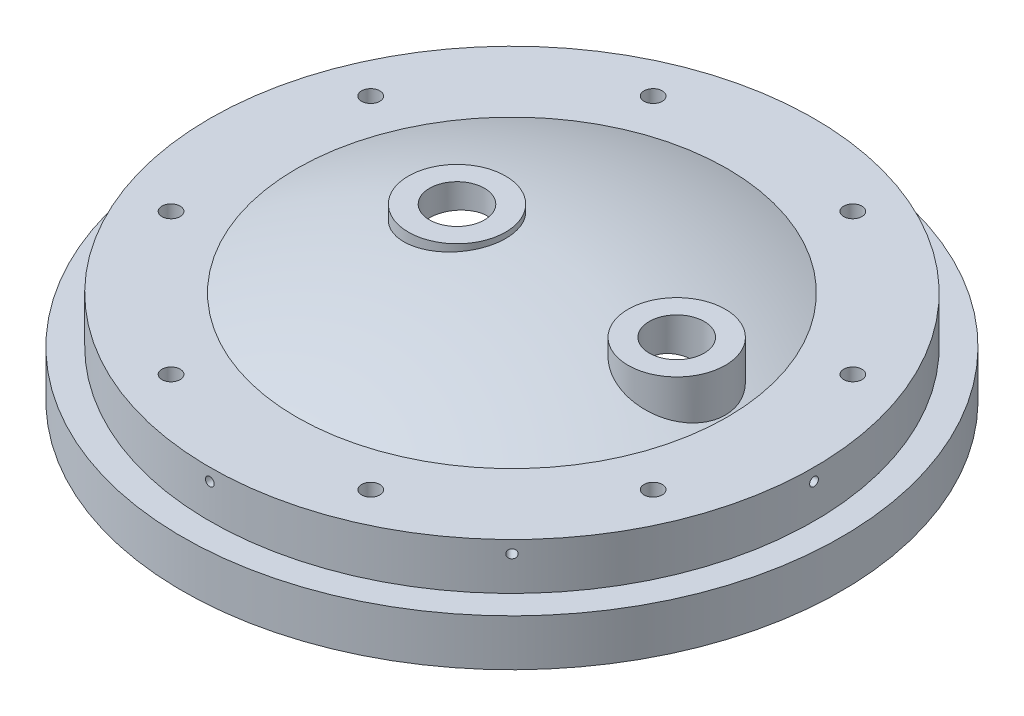
SolidWorks part; units mm, degrees
material "6061-T6 (SS)"
ref_plane "Front Plane" through (0, 0, 0) normal (0, 0, 1) x (1, 0, 0)
ref_plane "Top Plane" through (0, 0, 0) normal (0, 1, 0) x (1, 0, 0)
ref_plane "Right Plane" through (0, 0, 0) normal (1, 0, 0) x (0, 0, -1)
sketch "Sketch1" plane through (0, 0, 0) normal (0, 0, 1) x (1, 0, 0)
  line L0 (146.05, 0) -> (152.4, 0)
  line L1 (152.4, 0) -> (152.4, 21.59)
  line L2 (152.4, 21.59) -> (139.7, 21.59)
  line L3 (139.7, 21.59) -> (139.7, 43.18)
  line L4 (0, 63.5) -> (0, 57.15)
  line L5 (146.05, 0) -> (146.05, 9.4998)
  line L6 (139.7, 43.18) -> (99.5473, 43.18)
  arc A0 (0, 63.5) -> (99.5473, 43.18) centre (0, -190.5) cw
  arc A1 (0, 57.15) -> (146.05, 9.4998) centre (0, -190.5) cw
  dimension "D1" = 152.4
  dimension "D2" = 6.35
  dimension "D7" = 247.65
  dimension "D3" = 12.7
  dimension "D4" = 21.59
  dimension "D5" = 43.18
  dimension "D6" = 6.35
  dimension "D8" = 63.5
revolve "Revolve1" add sketch "Sketch1" angle 360 about L4
ref_plane "Plane1" through (139.7, 0, 0) normal (1, 0, 0) x (0, 0, -1)
hole_wizard "Tap Drill for #10-32 Tap1" positions "Sketch4" profile "Sketch5" hole size "#10-32" standard "ANSI Inch"
sketch "Sketch4" plane through (139.7, 0, 0) normal (1, 0, 0) x (0, 0, -1)
  line L0 (152.4, 21.59) -> (-152.4, 21.59) construction
  point P0 (0, 37.465)
  dimension "D1" = 15.875
sketch "Sketch5" plane through (139.7, 37.465, 0) normal (0, 1, 0) x (0, 0, -1)
  line L0 (0, 0) -> (0, 11.3733)
  line L1 (0, 11.3733) -> (2.0193, 10.16)
  line L2 (2.0193, 10.16) -> (2.0193, 0)
  line L5 (2.0193, 0) -> (0, 0)
  line L10 (0, 11.3733) -> (-2.0193, 10.16) construction
  line L11 (0, -6.35) -> (0, 107.95) construction
  dimension "Hole Dia." = 4.0386
  dimension "Hole Depth" = 10.16
  dimension "Drill Angle" = 118
pattern_circular "CirPattern1" count 8 over 360 about axis through (0, 63.5, 0) along (0, 1, 0) of "Tap Drill for #10-32 Tap1"
ref_plane "Plane2" through (0, 63.5, 0) normal (0, 1, 0) x (1, 0, 0)
sketch "Sketch6" plane through (0, 63.5, 0) normal (0, 1, 0) x (1, 0, 0)
  line L0 (-25.4, 0) -> (0, 0) construction
  circle A0 centre (-25.4, 0) radius 22.479
  dimension "D1" = 44.958
  dimension "D2" = 25.4
extrude "Boss-Extrude1" add sketch "Sketch6" along normal blind 2.54 and the other way up to next
sketch "Sketch7" plane through (0, 63.5, 0) normal (0, 1, 0) x (1, 0, 0)
  line L0 (76.2, 0) -> (0, 0) construction
  circle A0 centre (76.2, 0) radius 22.479
  dimension "D1" = 76.2
  dimension "D2" = 44.958
extrude "Boss-Extrude2" add sketch "Sketch7" against normal up to next
hole_wizard "Hole1" positions "Sketch8" profile "Sketch9" legacy
sketch "Sketch8" plane through (0, 66.04, 0) normal (0, 1, 0) x (1, 0, 0)
  point P0 (-25.4, 0)
sketch "Sketch9" plane through (-25.4, 66.04, 0) normal (1, 0, 0) x (0, 0, 1)
  line L0 (0, 0) -> (0, 25.4)
  line L1 (0, 25.4) -> (12.7, 25.4)
  line L2 (12.7, 25.4) -> (12.7, 0)
  line L3 (12.7, 0) -> (0, 0)
  line L4 (0, 110) -> (0, -10) construction
  dimension "Diameter" = 25.4
  dimension "Depth" = 25.4
hole_wizard "Hole2" positions "Sketch12" profile "Sketch13" legacy
sketch "Sketch12" plane through (0, 63.5, 0) normal (0, 1, 0) x (1, 0, 0)
  point P0 (76.2, 0)
sketch "Sketch13" plane through (76.2, 63.5, 0) normal (1, 0, 0) x (0, 0, 1)
  line L0 (0, 0) -> (0, 25.4)
  line L1 (0, 25.4) -> (12.7, 25.4)
  line L2 (12.7, 25.4) -> (12.7, 0)
  line L3 (12.7, 0) -> (0, 0)
  line L4 (0, 110) -> (0, -10) construction
  dimension "Diameter" = 25.4
  dimension "Depth" = 25.4
hole_wizard "3/8-24 Tapped Hole1" positions "Sketch15" profile "Sketch16" tap size "3/8-24" standard "ANSI Inch"
sketch "Sketch15" plane through (0, 43.18, 0) normal (0, 1, 0) x (1, 0, 0)
  line L0 (0, 0) -> (111.4661, 46.1708)
  line L2 (0, 0) -> (139.7, 0)
  circle A0 centre (0, 0) radius 139.7 construction
  point P0 (111.4661, 46.1708)
  dimension "D2" = 120.65
  dimension "D1" = 22.5
sketch "Sketch16" plane through (111.4661, 43.18, -46.1708) normal (1, 0, 0) x (0, 0, 1)
  line L0 (0, 0) -> (0, 12.1855)
  line L1 (0, 12.1855) -> (4.2164, 9.652)
  line L2 (4.2164, 9.652) -> (4.2164, 0)
  line L5 (4.2164, 0) -> (0, 0)
  line L10 (0, 12.1855) -> (-4.2164, 9.652) construction
  line L11 (0, -6.35) -> (0, 107.95) construction
  dimension "Tap Drill Dia." = 8.4328
  dimension "Tap Drill Depth" = 9.652
  dimension "Drill Angle" = 118
cosmetic thread "Hole Thread1" parameters "D1"=9.652, "D2"=9.525
pattern_circular "CirPattern2" count 8 over 360 about axis through (0, 0, 0) along (0, 1, 0) of "3/8-24 Tapped Hole1"
